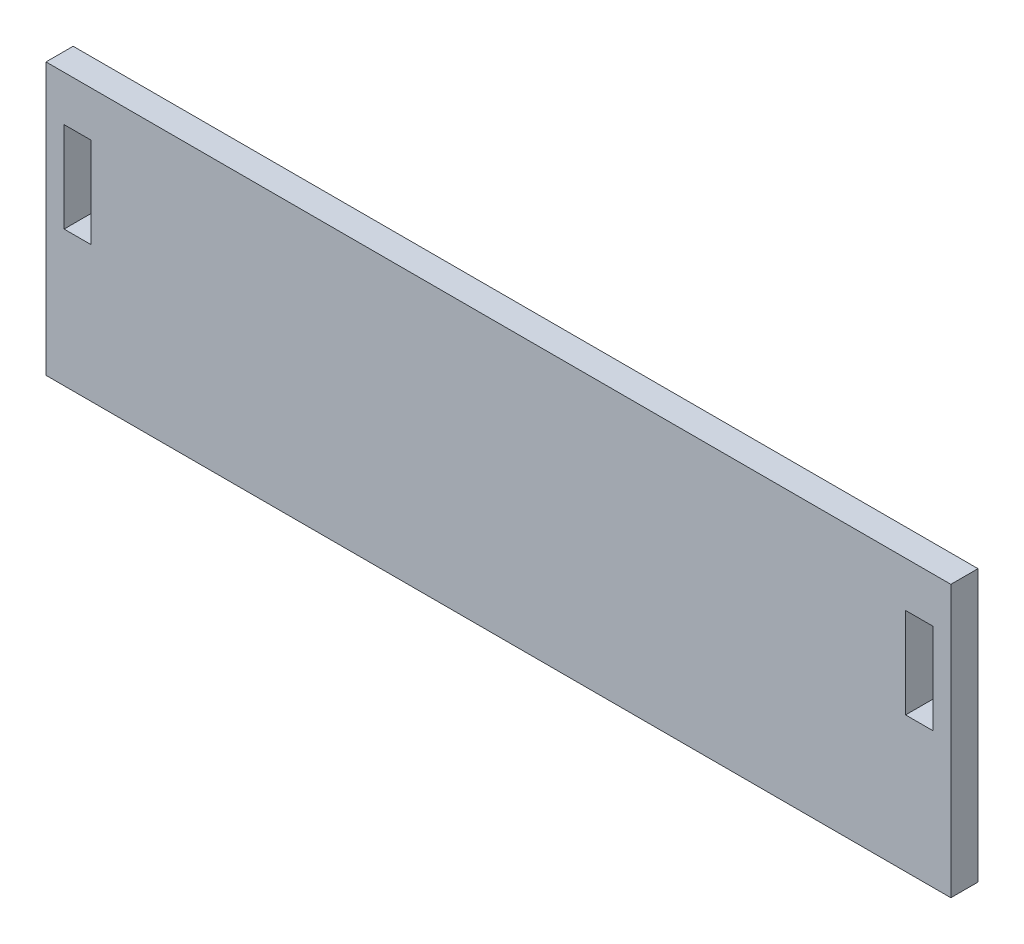
SolidWorks part; units mm, degrees
ref_plane "Front Plane" through (0, 0, 0) normal (0, 0, 1) x (1, 0, 0)
ref_plane "Top Plane" through (0, 0, 0) normal (0, 1, 0) x (1, 0, 0)
ref_plane "Right Plane" through (0, 0, 0) normal (1, 0, 0) x (0, 0, -1)
sketch "Sketch1" plane through (0, 0, 0) normal (0, 0, 1) x (1, 0, 0)
  line L1 (50, 15) -> (-50, 15)
  line L2 (50, 15) -> (50, -15)
  line L3 (50, -15) -> (-50, -15)
  line L4 (-50, 15) -> (-50, -15)
  line L7 (-48, 10) -> (-45, 10)
  line L8 (-48, 10) -> (-48, 0)
  line L9 (-48, 0) -> (-45, 0)
  line L10 (-45, 10) -> (-45, 0)
  line L13 (45, 0) -> (48, 0)
  line L14 (48, 10) -> (48, 0)
  line L16 (45, 10) -> (48, 10)
  line L17 (45, 10) -> (45, 0)
  point P0 (0, 0)
  point P6 (-46.5, 5)
  point P11 (46.5, 5)
  dimension "D1" = 100
  dimension "D2" = 30
extrude "Boss-Extrude1" add sketch "Sketch1" along normal blind 3
